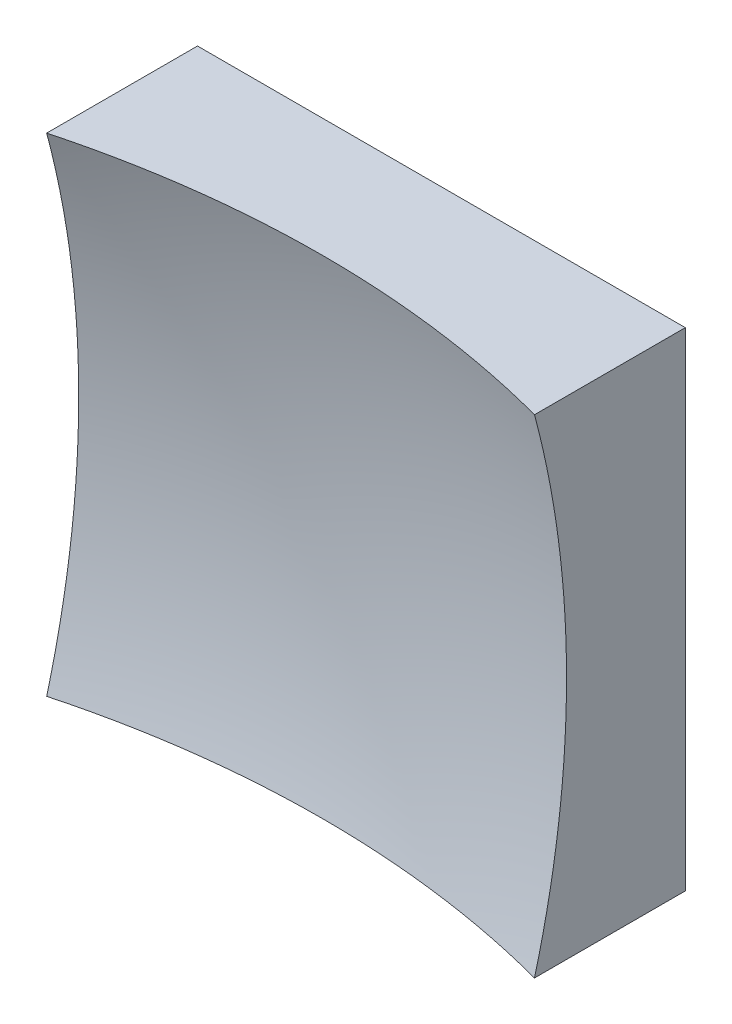
SolidWorks part; units mm, degrees
ref_plane "前视基准面" through (0, 0, 0) normal (0, 0, 1) x (1, 0, 0)
ref_plane "上视基准面" through (0, 0, 0) normal (0, 1, 0) x (1, 0, 0)
ref_plane "右视基准面" through (0, 0, 0) normal (1, 0, 0) x (0, 0, -1)
sketch "草图1" plane through (0, 0, 0) normal (0, 0, 1) x (1, 0, 0)
  line L1 (-25, 25) -> (25, 25)
  line L2 (-25, 25) -> (-25, -25)
  line L3 (-25, -25) -> (25, -25)
  line L4 (25, 25) -> (25, -25)
  line L5 (-25, 25) -> (25, -25) construction
  line L6 (-25, -25) -> (25, 25) construction
  point P0 (0, 0)
  dimension "D1" = 50
  dimension "D2" = 50
extrude "凸台-拉伸1" add sketch "草图1" along normal blind 50 contours L2 L3 L4 L1
sketch "草图2" plane through (0, 0, 0) normal (0, 1, 0) x (1, 0, 0)
  line L0 (-7.4603, -9) -> (7.3192, -9) construction
  line L1 (0, 0) -> (0, -12.1749) construction
  line L2 (97.4845, -86.7118) -> (0, -86.7118)
  line L3 (0, -86.7118) -> (0, -9)
  arc A1 (97.4845, -86.7118) -> (0, -9) centre (0, -109) ccw
  dimension "D2" = 200
  dimension "D1" = 9
revolve "切除-旋转2" cut sketch "草图2" angle 360 about L3
